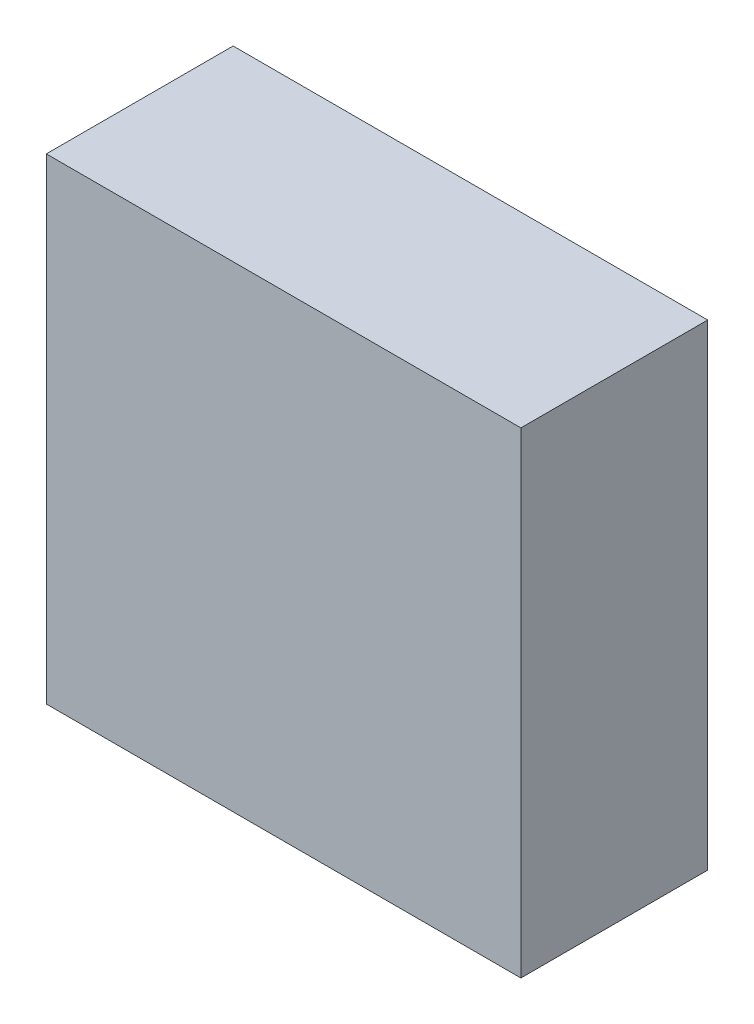
SolidWorks part; units mm, degrees
ref_plane "Front Plane" through (0, 0, 0) normal (0, 0, 1) x (1, 0, 0)
ref_plane "Top Plane" through (0, 0, 0) normal (0, 1, 0) x (1, 0, 0)
ref_plane "Right Plane" through (0, 0, 0) normal (1, 0, 0) x (0, 0, -1)
sketch "Esquisse1" plane through (0, 0, 0) normal (0, 0, 1) x (1, 0, 0)
  line L1 (-12.7, 12.75) -> (12.7, 12.75)
  line L2 (-12.7, 12.75) -> (-12.7, -12.75)
  line L3 (-12.7, -12.75) -> (12.7, -12.75)
  line L4 (12.7, 12.75) -> (12.7, -12.75)
  point P4 (-12.7, 0)
  point P6 (0, 12.75)
  point P7 (0, 0)
  point P9 (0, 0)
  dimension "D1" = 25.5
  dimension "D2" = 25.4
extrude "Boss.-Extru.1" add sketch "Esquisse1" along normal blind 10
